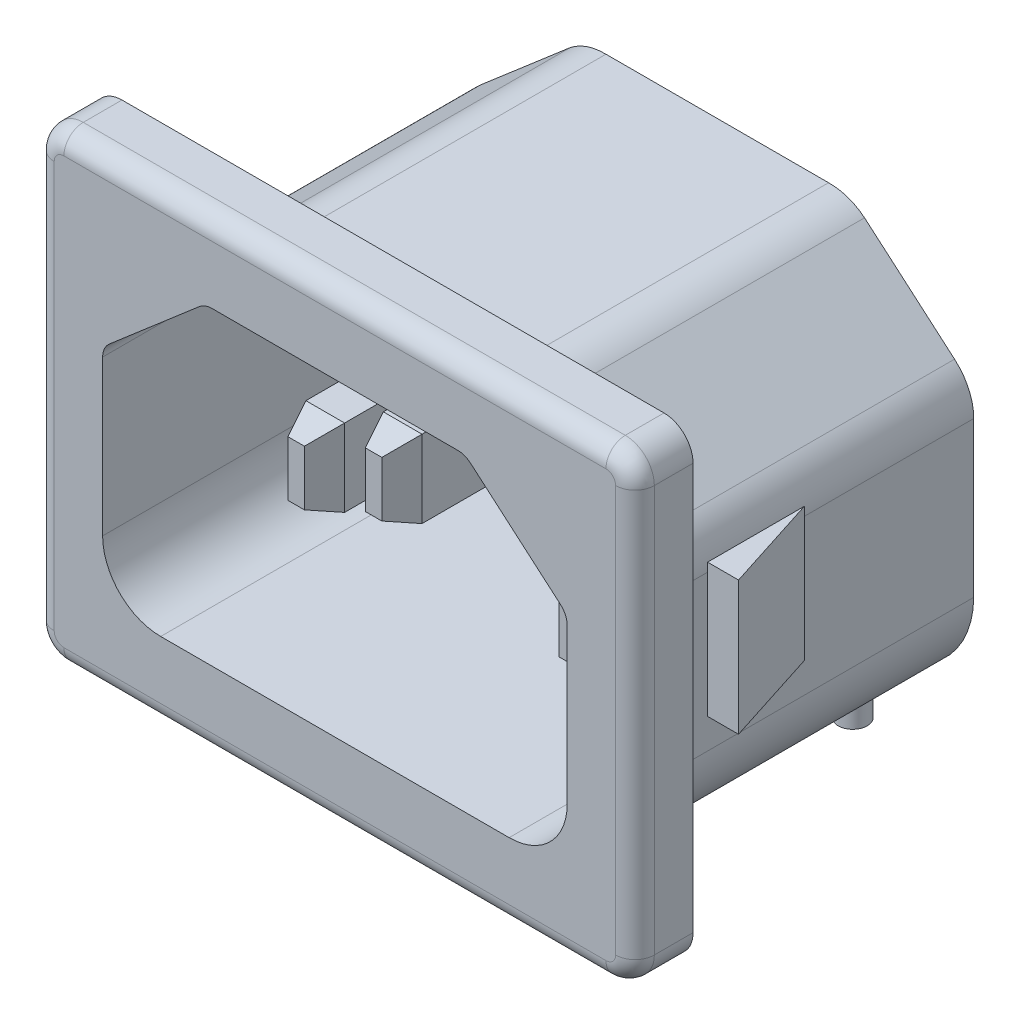
SolidWorks part; units mm, degrees
ref_plane "Front Plane" through (0, 0, 0) normal (0, 0, 1) x (1, 0, 0)
ref_plane "Top Plane" through (0, 0, 0) normal (0, 1, 0) x (1, 0, 0)
ref_plane "Right Plane" through (0, 0, 0) normal (1, 0, 0) x (0, 0, -1)
sketch "Sketch1" plane through (0, 0, 0) normal (0, 0, 1) x (1, 0, 0)
  line L0 (0, 0) -> (0, 63.1664) construction
  line L1 (0, 0) -> (65.5401, 0) construction
  line L3 (-14, -12) -> (14, -12)
  line L4 (-15.5, -10.5) -> (-15.5, 10.5)
  line L5 (-14, 12) -> (14, 12)
  line L6 (15.5, -10.5) -> (15.5, 10.5)
  arc A0 (-14, 12) -> (-15.5, 10.5) centre (-14, 10.5) ccw
  arc A1 (15.5, 10.5) -> (14, 12) centre (14, 10.5) ccw
  arc A2 (14, -12) -> (15.5, -10.5) centre (14, -10.5) ccw
  arc A3 (-15.5, -10.5) -> (-14, -12) centre (-14, -10.5) ccw
  point P10 (-15.5, 12)
  point P13 (15.5, 12)
  point P18 (-15.5, -12)
  dimension "D5" = 1.5
  dimension "D1" = 31
  dimension "D2" = 15.5
  dimension "D3" = 24
  dimension "D4" = 12
extrude "Extrude1" add sketch "Sketch1" along normal blind 19.75
sketch "Sketch2" plane through (0, 0, 19.75) normal (0, 0, 1) x (1, 0, 0)
  line L0 (0, -17.7613) -> (0, 20.0972) construction
  line L1 (-12, 3) -> (-12, -5)
  line L2 (-9, -8) -> (9, -8)
  line L3 (12, 3) -> (12, -5)
  line L4 (-11.6521, 3.7581) -> (-7.0021, 7.7581)
  line L5 (-6.35, 8) -> (6.35, 8)
  line L6 (11.6521, 3.7581) -> (7.0021, 7.7581)
  line L7 (14, 12) -> (-14, 12) construction
  arc A0 (-11.6521, 3.7581) -> (-12, 3) centre (-11, 3) ccw
  arc A1 (-6.35, 8) -> (-7.0021, 7.7581) centre (-6.35, 7) ccw
  arc A2 (7.0021, 7.7581) -> (6.35, 8) centre (6.35, 7) ccw
  arc A3 (12, 3) -> (11.6521, 3.7581) centre (11, 3) ccw
  arc A4 (-9, -8) -> (-12, -5) centre (-9, -5) cw
  arc A5 (12, -5) -> (9, -8) centre (9, -5) cw
  dimension "D1" = 1
  dimension "D7" = 3
  dimension "D2" = 24
  dimension "D3" = 12
  dimension "D4" = 16
  dimension "D5" = 4
  dimension "D6" = 11
  dimension "D8" = 12.7
  dimension "D9" = 6.35
extrude "Cut-Extrude1" cut sketch "Sketch2" against normal blind 17
sketch "Sketch3" plane through (0, 0, 0) normal (0, 0, -1) x (-1, 0, 0)
  line L0 (0, 16.9865) -> (0, -16.5626) construction
  line L1 (13.25, 3) -> (13.25, -5)
  line L2 (7.6086, 9.1606) -> (12.2586, 5.1606)
  line L3 (-14, 12) -> (14, 12) construction
  line L24 (5.75, 9.8) -> (-5.75, 9.8)
  line L25 (-7.6086, 9.1606) -> (-12.2586, 5.1606)
  line L26 (-13.25, 3) -> (-13.25, -5)
  line L27 (-8.4, -9.8) -> (8.4, -9.8)
  arc A0 (13.25, -5) -> (8.4, -9.8) centre (8.4003, -4.95) cw
  arc A1 (12.2586, 5.1606) -> (13.25, 3) centre (10.4, 3) cw
  arc A2 (5.75, 9.8) -> (7.6086, 9.1606) centre (5.809, 6.9506) cw
  arc A25 (-5.75, 9.8) -> (-7.6086, 9.1606) centre (-5.809, 6.9506) ccw
  arc A26 (-12.2586, 5.1606) -> (-13.25, 3) centre (-10.4, 3) ccw
  arc A27 (-13.25, -5) -> (-8.4, -9.8) centre (-8.4003, -4.95) ccw
  dimension "D1" = 26.5
  dimension "D2" = 19.6
  dimension "D3" = 2.2
extrude "Cut-Extrude2" cut sketch "Sketch3" against normal blind 16.75 flip side to cut
sketch "Sketch4" plane through (0, 0, 2.75) normal (0, 0, 1) x (1, 0, 0)
  line L0 (0, 18.3955) -> (0, -16.9209) construction
  line L1 (-1, 4.3) -> (-1, 0.3)
  line L2 (1, 4.3) -> (1, 0.3)
  line L3 (-1, 4.3) -> (1, 4.3)
  line L4 (-1, 0.3) -> (1, 0.3)
  line L5 (-7, -4.2) -> (-7, 2.8928) construction
  line L6 (-8, -0.2) -> (-6, -0.2)
  line L8 (-8, -4.2) -> (-6, -4.2)
  line L22 (-8, -0.2) -> (-8, -4.2)
  line L23 (-6, -0.2) -> (-6, -4.2)
  line L24 (7, -4.2) -> (7, 2.8928) construction
  line L39 (6, -0.2) -> (6, -4.2)
  line L40 (8, -4.2) -> (6, -4.2)
  line L41 (8, -0.2) -> (8, -4.2)
  line L42 (8, -0.2) -> (6, -0.2)
  line L43 (1, 2.3) -> (-4.2223, 2.3) construction
  line L44 (8, -2.2) -> (-8, -2.2) construction
  line L45 (6.35, 8) -> (-6.35, 8) construction
  dimension "D1" = 4
  dimension "D2" = 2
  dimension "D3" = 14
  dimension "D4" = 5.7
  dimension "D5" = 4.5
extrude "Extrude2" add sketch "Sketch4" along normal blind 15
sketch "Sketch5" plane through (0, 0, 17.75) normal (0, 0, 1) x (1, 0, 0)
  line L0 (8, -4.2) -> (8, -0.2) construction
  line L1 (6, -4.2) -> (8, -4.2) construction
  line L2 (6, -0.2) -> (6, -4.2) construction
  line L3 (8, -0.2) -> (6, -0.2) construction
  line L4 (-6, -4.2) -> (-6, -0.2) construction
  line L5 (-8, -4.2) -> (-6, -4.2) construction
  line L6 (-8, -0.2) -> (-8, -4.2) construction
  line L7 (-6, -0.2) -> (-8, -0.2) construction
  line L8 (8, -4.2) -> (8, -0.2)
  line L9 (6, -4.2) -> (8, -4.2)
  line L10 (6, -0.2) -> (6, -4.2)
  line L11 (8, -0.2) -> (6, -0.2)
  line L12 (-6, -4.2) -> (-6, -0.2)
  line L13 (-8, -4.2) -> (-6, -4.2)
  line L14 (-8, -0.2) -> (-8, -4.2)
  line L15 (-6, -0.2) -> (-8, -0.2)
extrude "Cut-Extrude3" cut sketch "Sketch5" against normal blind 3
chamfer "Chamfer1" distance 1.5 angle 21 12 edges at (8, -2.2, 14.75) (7, -4.2, 14.75) (6, -2.2, 14.75) (7, -0.2, 14.75) (0, 0.3, 17.75) (1, 2.3, 17.75) (0, 4.3, 17.75) (-1, 2.3, 17.75) (-6, -2.2, 14.75) (-7, -4.2, 14.75) (-8, -2.2, 14.75) (-7, -0.2, 14.75)
fillet "Fillet1" radius 1 8 edges at (15.0607, 11.5607, 19.75) (15.5, 0, 19.75) (15.0607, -11.5607, 19.75) (0, -12, 19.75) (-15.0607, -11.5607, 19.75) (-15.5, 0, 19.75) (-15.0607, 11.5607, 19.75) (0, 12, 19.75)
sketch "Sketch6" plane through (0, 0, 0) normal (0, 1, 0) x (1, 0, 0)
  line L0 (13.25, -16.75) -> (13.25, 0) construction
  line L1 (13.25, -13.75) -> (13.25, -8.75)
  line L2 (0, 3.3452) -> (0, -4.0073) construction
  line L3 (13.25, -13.75) -> (14.85, -13.75)
  line L4 (14.85, -13.75) -> (13.25, -8.75)
  line L5 (-14, -16.75) -> (14, -16.75) construction
  line L6 (-14.85, -13.75) -> (-13.25, -8.75)
  line L7 (-13.25, -13.75) -> (-14.85, -13.75)
  line L8 (-13.25, -13.75) -> (-13.25, -8.75)
  dimension "D1" = 3
  dimension "D2" = 5
  dimension "D3" = 29.7
extrude "Extrude3" add sketch "Sketch6" along normal mid plane 6.9
sketch "Sketch7" plane through (0, 0, 0) normal (0, 0, -1) x (-1, 0, 0)
  line L0 (0, 0) -> (0, -15.1502) construction
  line L1 (-2, -9.3) -> (-2, 5.7)
  line L2 (-9, -9.3) -> (-5, -9.3)
  line L3 (-9, -9.3) -> (-9, 1.7)
  line L4 (-9, 1.7) -> (-5, 1.7)
  line L5 (-5, -9.3) -> (-5, 1.7)
  line L6 (5, -9.3) -> (5, 1.7)
  line L7 (9, 1.7) -> (5, 1.7)
  line L8 (9, -9.3) -> (9, 1.7)
  line L9 (9, -9.3) -> (5, -9.3)
  line L10 (2, -9.3) -> (2, 5.7)
  line L11 (-2, 5.7) -> (2, 5.7)
  line L12 (-2, -9.3) -> (2, -9.3)
  line L13 (-7, -9.3) -> (-7, 14.9886) construction
  line L14 (-8.4, -9.8) -> (8.4, -9.8) construction
  dimension "D1" = 11
  dimension "D2" = 15
  dimension "D3" = 4
  dimension "D4" = 7
  dimension "D5" = 0.5
extrude "Extrude4" add sketch "Sketch7" along normal blind 2
sketch "Sketch8" plane through (0, -9.3, 0) normal (0, -1, 0) x (1, 0, 0)
  line L0 (-14, 19.75) -> (14, 19.75) construction
  circle A0 centre (7, 0) radius 0.75
  circle A1 centre (0, 0) radius 0.75
  circle A2 centre (-7, 0) radius 0.75
  dimension "D3" = 1.5
  dimension "D1" = 14
  dimension "D2" = 7
  dimension "D4" = 19.75
extrude "Extrude5" add sketch "Sketch8" along normal blind 4.2
equation "\"D2@Sketch1\" = \"D1@Sketch1\" / 2"
equation "\"D4@Sketch1\" = \"D3@Sketch1\" / 2"
equation "\"D3@Sketch2\" = \"D2@Sketch2\" / 2"
equation "\"D9@Sketch2\" = \"D8@Sketch2\" / 2"
